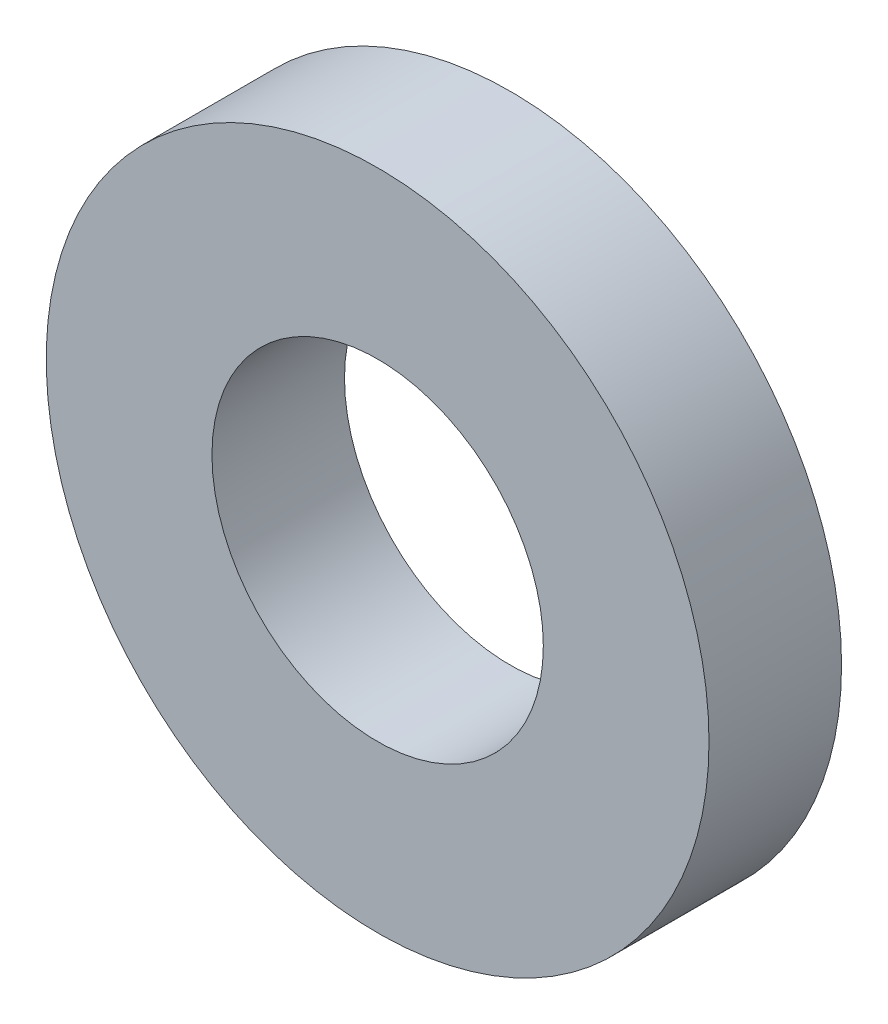
SolidWorks part; units mm, degrees
ref_plane "Front Plane" through (0, 0, 0) normal (0, 0, 1) x (1, 0, 0)
ref_plane "Top Plane" through (0, 0, 0) normal (0, 1, 0) x (1, 0, 0)
ref_plane "Right Plane" through (0, 0, 0) normal (1, 0, 0) x (0, 0, -1)
sketch "Sketch1" plane through (0, 0, 0) normal (0, 0, 1) x (1, 0, 0)
  circle A0 centre (0, 0) radius 3.175
  circle A1 centre (0, 0) radius 6.35
  dimension "D1" = 6.35
  dimension "D2" = 12.7
extrude "Boss-Extrude1" add sketch "Sketch1" along normal blind 2.54
